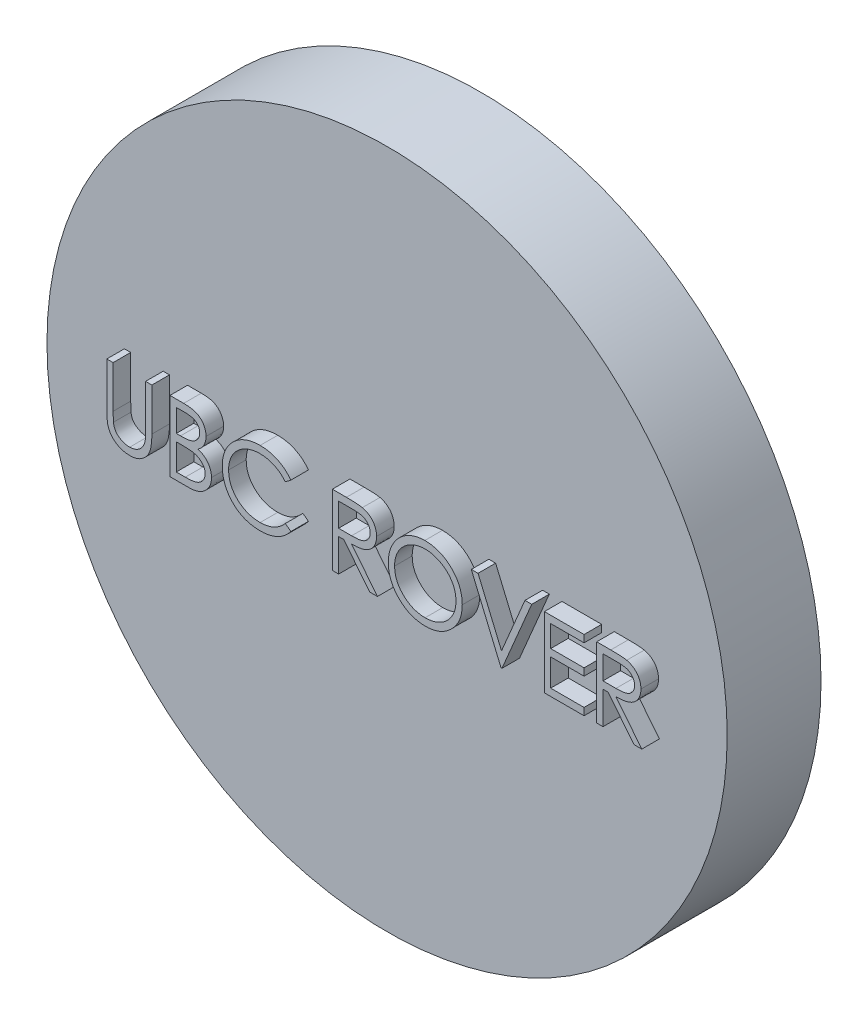
SolidWorks part; units mm, degrees
ref_plane "Front Plane" through (0, 0, 0) normal (0, 0, 1) x (1, 0, 0)
ref_plane "Top Plane" through (0, 0, 0) normal (0, 1, 0) x (1, 0, 0)
ref_plane "Right Plane" through (0, 0, 0) normal (1, 0, 0) x (0, 0, -1)
sketch "Sketch1" plane through (0, 0, 0) normal (0, 0, 1) x (1, 0, 0)
  circle A0 centre (0, 0) radius 29
  dimension "D1" = 58
extrude "Plate" add sketch "Sketch1" along normal blind 8
sketch "Sketch4" plane through (0, 0, 8) normal (0, 0, 1) x (1, 0, 0)
  text T0 "UBC ROVER" font "Century Gothic" height 6
  point P1 (0, 0)
  point P2 (0, 0)
extrude "Boss-Extrude4" add sketch "Sketch4" along normal blind 1.5
